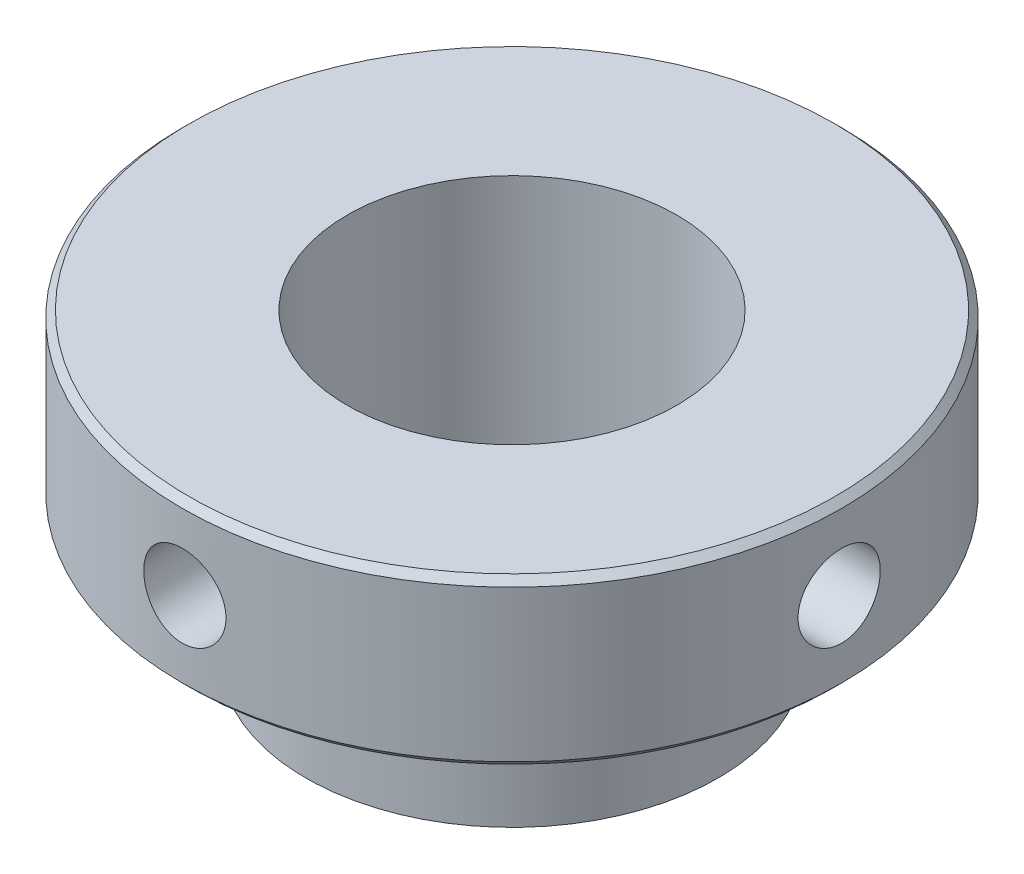
SolidWorks part; units mm, degrees
material "Plain Carbon Steel"
ref_plane "Front Plane" through (0, 0, 0) normal (0, 0, 1) x (1, 0, 0)
ref_plane "Top Plane" through (0, 0, 0) normal (0, 1, 0) x (1, 0, 0)
ref_plane "Right Plane" through (0, 0, 0) normal (1, 0, 0) x (0, 0, -1)
sketch "Sketch1" plane through (0, 0, 0) normal (0, 0, 1) x (1, 0, 0)
  line L0 (1.5, 0) -> (1.5, 2.75)
  line L1 (1.5, 2.75) -> (2.938, 2.75)
  line L2 (3, 2.688) -> (3, 1.312)
  line L3 (2.938, 1.25) -> (1.875, 1.25)
  line L4 (1.875, 1.25) -> (1.875, 0)
  line L5 (1.875, 0) -> (1.5, 0)
  line L6 (0, 0) -> (0, 2.75) construction
  line L7 (2.938, 2.75) -> (3, 2.688)
  line L8 (3, 1.312) -> (2.938, 1.25)
  point P4 (3, 2.75)
  point P5 (3, 1.25)
  dimension "D1" = 2.75
  dimension "D2" = 1.5
  dimension "D3" = 3
  dimension "D4" = 1.875
  dimension "D5" = 1.5
  dimension "D6" = 0.062
  dimension "D7" = 45
  dimension "D8" = 0.062
  dimension "D9" = 45
revolve "Revolve2" add sketch "Sketch1" angle 360 about L6
sketch "Sketch4" plane through (0, 0, 0) normal (0, 0, 1) x (1, 0, 0)
  line L0 (-3.475, 2) -> (-1.875, 2) construction
  line L1 (-3.475, 2.374) -> (-2.175, 2.374)
  line L2 (3, 2.75) -> (-3, 2.75) construction
  line L3 (-3.475, 2.374) -> (-1.875, 2.374) construction
  line L4 (-2.175, 2.374) -> (-1.875, 2)
  line L5 (-3.475, 2) -> (-3.475, 2.374)
  line L6 (-3.475, 2) -> (-1.875, 2)
  dimension "D1" = 0.374
  dimension "D2" = 0.75
  dimension "D3" = 1.3
  dimension "D4" = 0.3
revolve "Cut-Revolve1" cut sketch "Sketch4" angle 360 about L6
pattern_circular "CirPattern1" count 4 over 360 about axis through (0, 2.75, 0) along (0, -1, 0) of "Cut-Revolve1"
